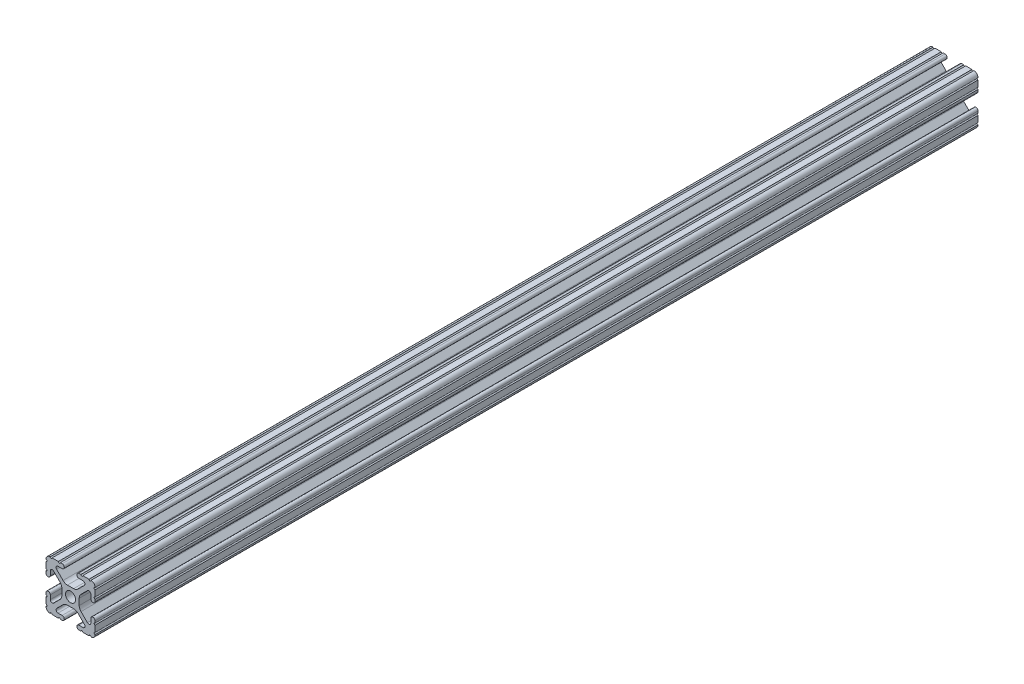
SolidWorks part; units mm, degrees
ref_plane "Front Plane" through (0, 0, 0) normal (0, 0, 1) x (1, 0, 0)
ref_plane "Top Plane" through (0, 0, 0) normal (0, 1, 0) x (1, 0, 0)
ref_plane "Right Plane" through (0, 0, 0) normal (1, 0, 0) x (0, 0, -1)
ref_plane "Plane1" through (0, 0, -450.85) normal (0, 0, -1) x (-1, 0, 0)
sketch "Sketch1" plane through (0, 0, -450.85) normal (0, 0, -1) x (-1, 0, 0)
  line L0 (12.7, -9.5504) -> (12.7, -6.3331)
  line L1 (12.7, -5.3171) -> (12.7, -4.3434)
  line L2 (10.4902, -4.3434) -> (10.4902, -6.4748)
  line L3 (8.7558, -7.1932) -> (5.4257, -3.8632)
  line L4 (4.4958, -1.6181) -> (4.4958, 1.6181)
  line L5 (5.4257, 3.8632) -> (8.7558, 7.1932)
  line L6 (10.4902, 6.4748) -> (10.4902, 4.3434)
  line L7 (12.7, 4.3434) -> (12.7, 5.3171)
  line L8 (12.7, 6.3331) -> (12.7, 9.5504)
  line L9 (9.5504, 12.7) -> (6.3331, 12.7)
  line L10 (5.3171, 12.7) -> (4.3434, 12.7)
  line L11 (4.3434, 10.4902) -> (6.4748, 10.4902)
  line L12 (7.1932, 8.7558) -> (3.8632, 5.4257)
  line L13 (1.6181, 4.4958) -> (-1.6181, 4.4958)
  line L14 (-3.8632, 5.4257) -> (-7.1932, 8.7558)
  line L15 (-6.4748, 10.4902) -> (-4.3434, 10.4902)
  line L16 (-4.3434, 12.7) -> (-5.3171, 12.7)
  line L17 (-6.3331, 12.7) -> (-9.5504, 12.7)
  line L18 (-12.7, 9.5504) -> (-12.7, 6.3331)
  line L19 (-12.7, 5.3171) -> (-12.7, 4.3434)
  line L20 (-10.4902, 4.3434) -> (-10.4902, 6.4748)
  line L21 (-8.7558, 7.1932) -> (-5.4257, 3.8632)
  line L22 (-4.4958, 1.6181) -> (-4.4958, -1.6181)
  line L23 (-5.4257, -3.8632) -> (-8.7558, -7.1932)
  line L24 (-10.4902, -6.4748) -> (-10.4902, -4.3434)
  line L25 (-12.7, -4.3434) -> (-12.7, -5.3171)
  line L26 (-12.7, -6.3331) -> (-12.7, -9.5504)
  line L27 (-9.5504, -12.7) -> (-6.3331, -12.7)
  line L28 (-5.3171, -12.7) -> (-4.3434, -12.7)
  line L29 (-4.3434, -10.4902) -> (-6.4748, -10.4902)
  line L30 (-7.1932, -8.7558) -> (-3.8632, -5.4257)
  line L31 (-1.6181, -4.4958) -> (1.6181, -4.4958)
  line L32 (3.8632, -5.4257) -> (7.1932, -8.7558)
  line L33 (6.4748, -10.4902) -> (4.3434, -10.4902)
  line L34 (4.3434, -12.7) -> (5.3171, -12.7)
  line L35 (6.3331, -12.7) -> (9.5504, -12.7)
  arc A0 (12.6998, -10.5664) -> (12.7, -9.5504) centre (12.7, -10.0584) cw
  arc A1 (12.7, -6.3331) -> (12.7, -5.3171) centre (12.7, -5.8251) cw
  arc A2 (12.7, -4.3434) -> (10.4902, -4.3434) centre (11.5951, -4.3434) ccw
  arc A3 (10.4902, -6.4748) -> (8.7558, -7.1932) centre (9.4742, -6.4748) cw
  arc A4 (5.4257, -3.8632) -> (4.4958, -1.6181) centre (7.6708, -1.6181) cw
  arc A5 (4.4958, 1.6181) -> (5.4257, 3.8632) centre (7.6708, 1.6181) cw
  arc A6 (8.7558, 7.1932) -> (10.4902, 6.4748) centre (9.4742, 6.4748) cw
  arc A7 (10.4902, 4.3434) -> (12.7, 4.3434) centre (11.5951, 4.3434) ccw
  arc A8 (12.7, 5.3171) -> (12.7, 6.3331) centre (12.7, 5.8251) cw
  arc A9 (12.7, 9.5504) -> (12.6998, 10.5664) centre (12.7, 10.0584) cw
  arc A10 (12.6998, 10.5664) -> (10.5664, 12.6998) centre (10.5918, 10.5918) ccw
  arc A11 (10.5664, 12.6998) -> (9.5504, 12.7) centre (10.0584, 12.7) cw
  arc A12 (6.3331, 12.7) -> (5.3171, 12.7) centre (5.8251, 12.7) cw
  arc A13 (4.3434, 12.7) -> (4.3434, 10.4902) centre (4.3434, 11.5951) ccw
  arc A14 (6.4748, 10.4902) -> (7.1932, 8.7558) centre (6.4748, 9.4742) cw
  arc A15 (3.8632, 5.4257) -> (1.6181, 4.4958) centre (1.6181, 7.6708) cw
  arc A16 (-1.6181, 4.4958) -> (-3.8632, 5.4257) centre (-1.6181, 7.6708) cw
  arc A17 (-7.1932, 8.7558) -> (-6.4748, 10.4902) centre (-6.4748, 9.4742) cw
  arc A18 (-4.3434, 10.4902) -> (-4.3434, 12.7) centre (-4.3434, 11.5951) ccw
  arc A19 (-5.3171, 12.7) -> (-6.3331, 12.7) centre (-5.8251, 12.7) cw
  arc A20 (-9.5504, 12.7) -> (-10.5664, 12.6998) centre (-10.0584, 12.7) cw
  arc A21 (-10.5664, 12.6998) -> (-12.6998, 10.5664) centre (-10.5918, 10.5918) ccw
  arc A22 (-12.6998, 10.5664) -> (-12.7, 9.5504) centre (-12.7, 10.0584) cw
  arc A23 (-12.7, 6.3331) -> (-12.7, 5.3171) centre (-12.7, 5.8251) cw
  arc A24 (-12.7, 4.3434) -> (-10.4902, 4.3434) centre (-11.5951, 4.3434) ccw
  arc A25 (-10.4902, 6.4748) -> (-8.7558, 7.1932) centre (-9.4742, 6.4748) cw
  arc A26 (-5.4257, 3.8632) -> (-4.4958, 1.6181) centre (-7.6708, 1.6181) cw
  arc A27 (-4.4958, -1.6181) -> (-5.4257, -3.8632) centre (-7.6708, -1.6181) cw
  arc A28 (-8.7558, -7.1932) -> (-10.4902, -6.4748) centre (-9.4742, -6.4748) cw
  arc A29 (-10.4902, -4.3434) -> (-12.7, -4.3434) centre (-11.5951, -4.3434) ccw
  arc A30 (-12.7, -5.3171) -> (-12.7, -6.3331) centre (-12.7, -5.8251) cw
  arc A31 (-12.7, -9.5504) -> (-12.6998, -10.5664) centre (-12.7, -10.0584) cw
  arc A32 (-12.6998, -10.5664) -> (-10.5664, -12.6998) centre (-10.5918, -10.5918) ccw
  arc A33 (-10.5664, -12.6998) -> (-9.5504, -12.7) centre (-10.0584, -12.7) cw
  arc A34 (-6.3331, -12.7) -> (-5.3171, -12.7) centre (-5.8251, -12.7) cw
  arc A35 (-4.3434, -12.7) -> (-4.3434, -10.4902) centre (-4.3434, -11.5951) ccw
  arc A36 (-6.4748, -10.4902) -> (-7.1932, -8.7558) centre (-6.4748, -9.4742) cw
  arc A37 (-3.8632, -5.4257) -> (-1.6181, -4.4958) centre (-1.6181, -7.6708) cw
  arc A38 (1.6181, -4.4958) -> (3.8632, -5.4257) centre (1.6181, -7.6708) cw
  arc A39 (7.1932, -8.7558) -> (6.4748, -10.4902) centre (6.4748, -9.4742) cw
  arc A40 (4.3434, -10.4902) -> (4.3434, -12.7) centre (4.3434, -11.5951) ccw
  arc A41 (5.3171, -12.7) -> (6.3331, -12.7) centre (5.8251, -12.7) cw
  arc A42 (9.5504, -12.7) -> (10.5664, -12.6998) centre (10.0584, -12.7) cw
  arc A43 (10.5664, -12.6998) -> (12.6998, -10.5664) centre (10.5918, -10.5918) ccw
  circle A44 centre (0, 0) radius 2.6035
extrude "Boss-Extrude1" add sketch "Sketch1" against normal blind 457.2
